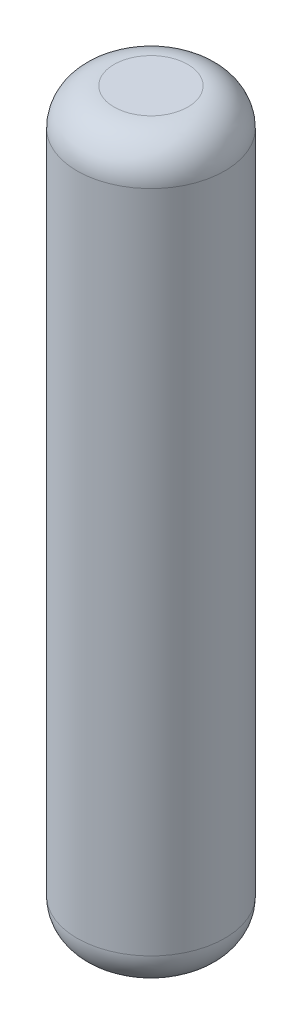
SolidWorks part; units mm, degrees
ref_plane "Alzado" through (0, 0, 0) normal (0, 0, 1) x (1, 0, 0)
ref_plane "Planta" through (0, 0, 0) normal (0, 1, 0) x (1, 0, 0)
ref_plane "Vista lateral" through (0, 0, 0) normal (1, 0, 0) x (0, 0, -1)
sketch "Croquis1" plane through (0, 0, 0) normal (0, 1, 0) x (1, 0, 0)
  circle A0 centre (0, 0) radius 2
extrude "Saliente-Extruir1" add sketch "Croquis1" along normal blind 20
fillet "Redondeo1" radius 1 2 edges at (0, 0, 2) (0, 20, 2)
